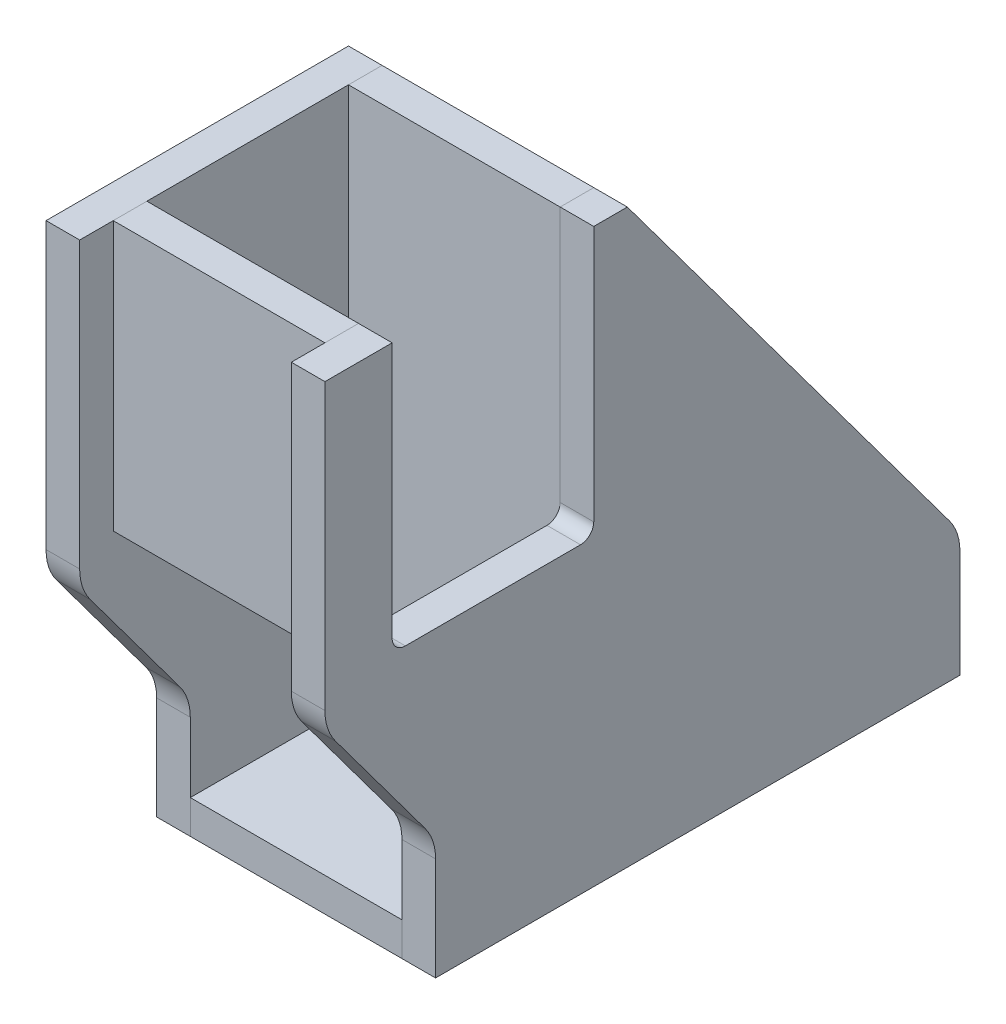
SolidWorks part; units mm, degrees
ref_plane "Front Plane" through (0, 0, 0) normal (0, 0, 1) x (1, 0, 0)
ref_plane "Top Plane" through (0, 0, 0) normal (0, 1, 0) x (1, 0, 0)
ref_plane "Right Plane" through (0, 0, 0) normal (1, 0, 0) x (0, 0, -1)
sketch "Sketch1" plane through (0, 0, 0) normal (1, 0, 0) x (0, 0, -1)
  line L16 (0, 0) -> (-240, 0)
  line L17 (0, 0) -> (0, 216.11)
  line L18 (0, 216.11) -> (-240, 216.11)
  line L19 (-240, 0) -> (-240, 216.11)
  dimension "D1" = 240
  dimension "D2" = 216.11
extrude "Boss-Extrude1" add sketch "Sketch1" along normal blind 12.7 from offset 40
mirror "Mirror3" about plane through (0, 0, 0) normal (1, 0, 0) of bodies 101
sketch "Sketch2" plane through (52.7, 0, 0) normal (1, 0, 0) x (0, 0, -1)
  line L0 (-125.7, 216.11) -> (0, 47.1708)
  line L1 (0, 216.11) -> (-240, 216.11) construction
  line L2 (0, 0) -> (0, 216.11) construction
  line L3 (0, 47.1708) -> (0, 216.11)
  line L4 (0, 216.11) -> (-125.7, 216.11)
  line L5 (-240, 101.81) -> (-198.1883, 45.6156)
  line L6 (-240, 216.11) -> (-240, 0) construction
  line L7 (-198.1883, 45.6156) -> (-198.1883, 0)
  line L8 (-240, 0) -> (0, 0) construction
  line L9 (-198.1883, 0) -> (-240, 0)
  line L10 (-240, 0) -> (-240, 101.81)
  dimension "D1" = 114.3
  dimension "D2" = 114.3
extrude "Cut-Extrude1" cut sketch "Sketch2" against normal through all both and the other way through all
sketch "Sketch3" plane through (52.7, 0, 0) normal (1, 0, 0) x (0, 0, -1)
  line L0 (0, 0) -> (0, 47.1708) construction
  line L1 (-198.1883, 0) -> (0, 0)
  line L2 (-198.1883, 0) -> (-198.1883, 12.7)
  line L3 (-198.1883, 12.7) -> (0, 12.7)
  line L4 (0, 0) -> (0, 12.7)
  dimension "D1" = 12.7
extrude "Boss-Extrude2" add sketch "Sketch3" against normal up to surface (80 mm away) from surface at -12.7 separate body up to face at (-40, 89.5452, 143.1538) starting at face at (40, 89.5452, 143.1538)
sketch "Sketch4" plane through (52.7, 0, 0) normal (1, 0, 0) x (0, 0, -1)
  line L0 (0, 12.7) -> (-198.1883, 12.7) construction
  line L1 (-125.7, 216.11) -> (-138.4, 216.11)
  line L2 (-125.7, 216.11) -> (-125.7, 12.7)
  line L3 (-125.7, 12.7) -> (-138.4, 12.7)
  line L4 (-138.4, 216.11) -> (-138.4, 12.7)
  dimension "D1" = 12.7
extrude "Boss-Extrude3" add sketch "Sketch4" against normal up to surface (80 mm away) from surface at -12.7 separate body up to face at (-40, 89.5452, 143.1538) starting at face at (40, 89.5452, 143.1538)
sketch "Sketch5" plane through (-40, 0, 0) normal (1, 0, 0) x (0, 0, -1)
  line L0 (-240, 216.11) -> (-240, 101.81) construction
  line L1 (-227.3, 216.11) -> (-214.6, 216.11)
  line L2 (-227.3, 216.11) -> (-227.3, 114.51)
  line L3 (-227.3, 114.51) -> (-214.6, 114.51)
  line L4 (-214.6, 216.11) -> (-214.6, 114.51)
  line L5 (-125.7, 216.11) -> (-240, 216.11) construction
  dimension "D1" = 101.6
  dimension "D2" = 12.7
  dimension "D3" = 12.7
extrude "Boss-Extrude4" add sketch "Sketch5" along normal up to surface (80 mm away) separate body up to face at (40, 89.5452, 143.1538)
sketch "Sketch7" plane through (0, 0, 0) normal (1, 0, 0) x (0, 0, -1)
  line L0 (-125.7, 216.11) -> (-240, 216.11) construction
  line L1 (-214.6, 216.11) -> (-138.4, 216.11)
  line L2 (-214.6, 216.11) -> (-214.6, 119.405)
  line L3 (-209.6, 114.405) -> (-143.4, 114.405)
  line L4 (-138.4, 216.11) -> (-138.4, 119.405)
  line L5 (-214.6, 114.51) -> (-214.6, 216.11) construction
  line L6 (-138.4, 216.11) -> (-138.4, 12.7) construction
  arc A0 (-214.6, 119.405) -> (-209.6, 114.405) centre (-209.6, 119.405) ccw
  arc A1 (-143.4, 114.405) -> (-138.4, 119.405) centre (-143.4, 119.405) ccw
  point P14 (-138.4, 114.405)
  dimension "D1" = 5
extrude "Cut-Extrude2" cut sketch "Sketch7" along normal blind 223.7
fillet "Fillet1" radius 20 3 edges at (46.35, 47.1708, 0) (46.35, 101.81, 240) (46.35, 45.6156, 198.1883)
fillet "Fillet2" radius 20 3 edges at (-46.35, 45.6156, 198.1883) (-46.35, 101.81, 240) (-46.35, 47.1708, 0)
